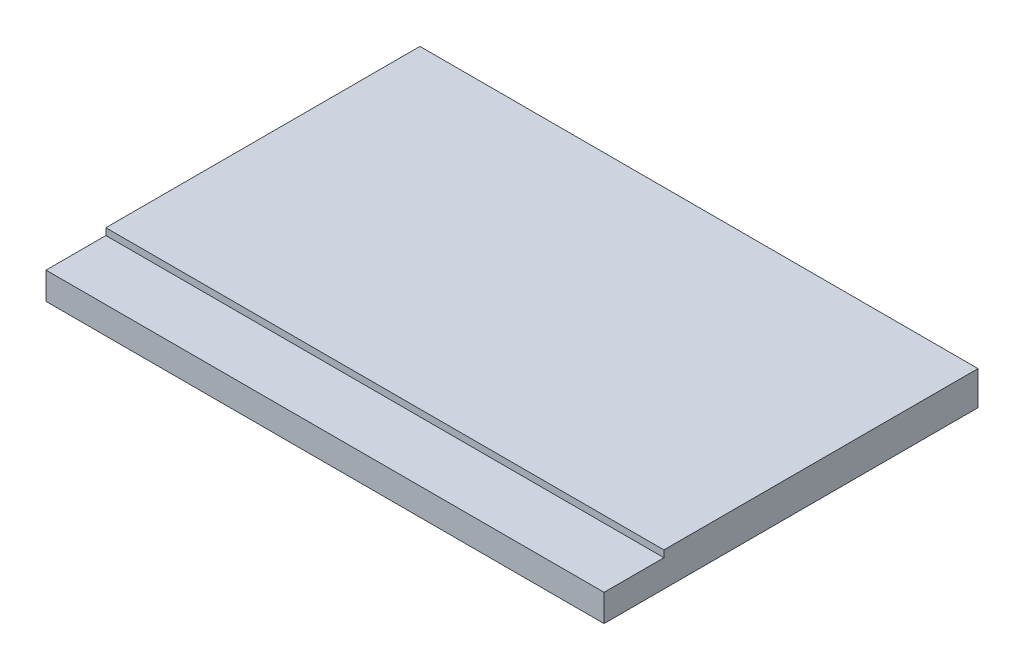
SolidWorks part; units mm, degrees
ref_plane "Front Plane" through (0, 0, 0) normal (0, 0, 1) x (1, 0, 0)
ref_plane "Top Plane" through (0, 0, 0) normal (0, 1, 0) x (1, 0, 0)
ref_plane "Right Plane" through (0, 0, 0) normal (1, 0, 0) x (0, 0, -1)
sketch "Sketch1" plane through (0, 0, 0) normal (0, 1, 0) x (1, 0, 0)
  line L1 (-12.35, -8.275) -> (12.35, -8.275)
  line L2 (-12.35, -8.275) -> (-12.35, 8.275)
  line L3 (-12.35, 8.275) -> (12.35, 8.275)
  line L4 (12.35, -8.275) -> (12.35, 8.275)
  line L5 (-12.35, -8.275) -> (12.35, 8.275) construction
  line L6 (-12.35, 8.275) -> (12.35, -8.275) construction
  point P0 (0, 0)
  dimension "D1" = 16.55
  dimension "D2" = 24.7
extrude "Boss-Extrude1" add sketch "Sketch1" along normal blind 1.5
sketch "Sketch2" plane through (0, 1.5, 0) normal (0, 1, 0) x (1, 0, 0)
  line L5 (12.35, -8.275) -> (12.35, 8.275) construction
  line L6 (-12.35, -8.275) -> (12.35, -8.275)
  line L8 (-12.35, -8.275) -> (-12.35, -5.625)
  line L9 (-12.35, -5.625) -> (12.35, -5.625)
  line L10 (12.35, -8.275) -> (12.35, -5.625)
  line L11 (-12.35, -8.275) -> (12.35, -5.625) construction
  line L12 (-12.35, -5.625) -> (12.35, -8.275) construction
  point P4 (0, -6.95)
  dimension "D1" = 2.65
extrude "Cut-Extrude1" cut sketch "Sketch2" against normal blind 0.3
